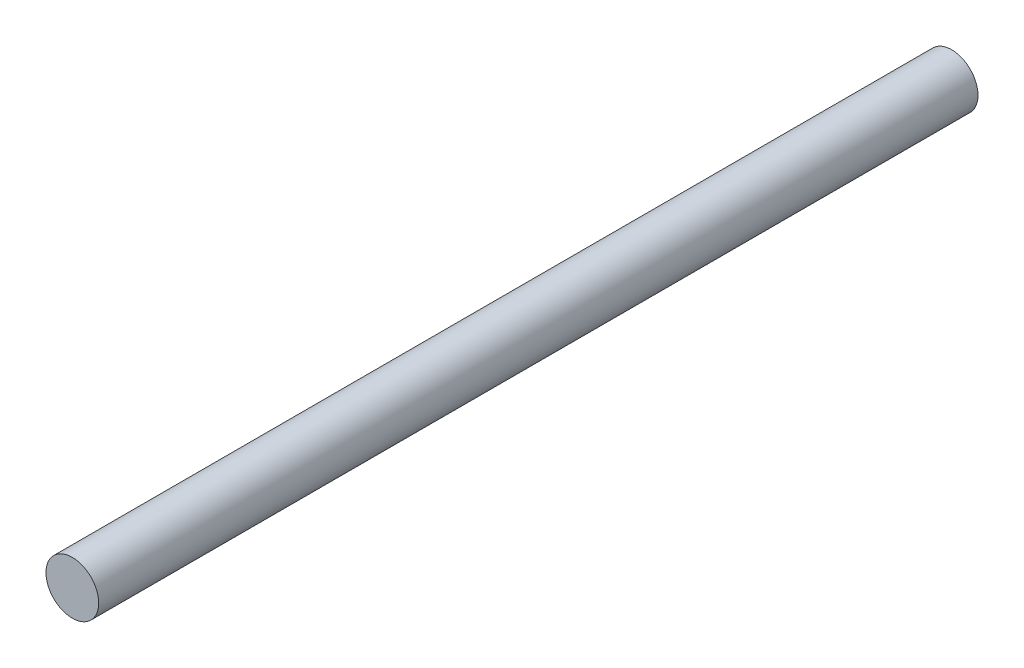
SolidWorks part; units mm, degrees
ref_plane "Plan de face" through (0, 0, 0) normal (0, 0, 1) x (1, 0, 0)
ref_plane "Plan de dessus" through (0, 0, 0) normal (0, 1, 0) x (1, 0, 0)
ref_plane "Plan de droite" through (0, 0, 0) normal (1, 0, 0) x (0, 0, -1)
sketch "Esquisse1" plane through (0, 0, 0) normal (0, 0, 1) x (1, 0, 0)
  circle A0 centre (0, 0) radius 1.5
  dimension "D1" = 3
extrude "Boss.-Extru.1" add sketch "Esquisse1" along normal blind 50
